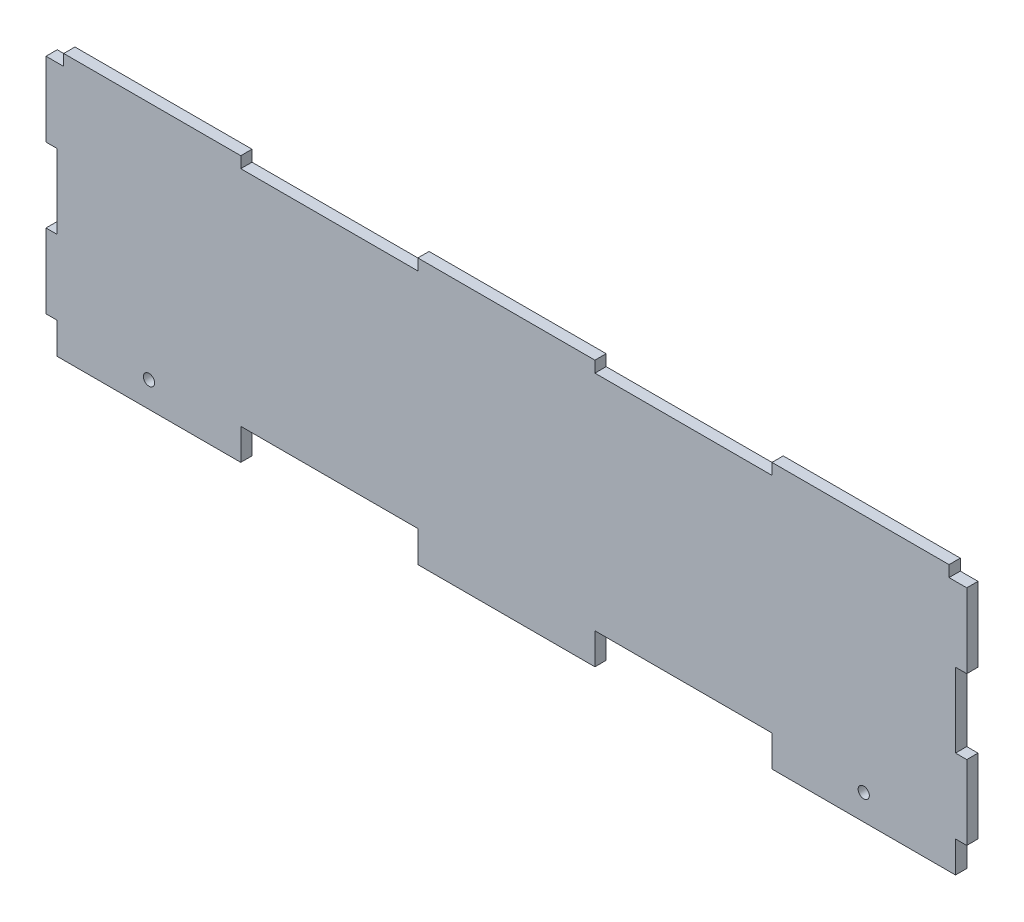
SolidWorks part; units mm, degrees
ref_plane "Front Plane" through (0, 0, 0) normal (0, 0, 1) x (1, 0, 0)
ref_plane "Top Plane" through (0, 0, 0) normal (0, 1, 0) x (1, 0, 0)
ref_plane "Right Plane" through (0, 0, 0) normal (1, 0, 0) x (0, 0, -1)
sketch "Sketch1" plane through (0, 0, 0) normal (0, 0, 1) x (1, 0, 0)
  line L0 (5, 71.825) -> (55, 71.825) construction
  line L1 (0, 75) -> (260, 75)
  line L2 (0, 75) -> (0, 0)
  line L3 (0, 0) -> (260, 0)
  line L4 (260, 75) -> (260, 0)
  line L5 (5, 75) -> (5, 71.825)
  line L6 (255, 75) -> (255, 71.825)
  line L7 (55, 71.825) -> (55, 75)
  line L8 (105, 75) -> (105, 71.825)
  line L9 (105, 71.825) -> (155, 71.825) construction
  line L10 (155, 71.825) -> (155, 75)
  line L11 (205, 71.825) -> (255, 71.825) construction
  line L12 (5, 71.825) -> (0, 71.825)
  line L13 (255, 71.825) -> (260, 71.825)
  line L14 (205, 71.825) -> (205, 75)
  line L15 (256.825, 75) -> (256.825, 0) construction
  line L16 (55, 71.825) -> (105, 71.825)
  line L17 (155, 71.825) -> (205, 71.825)
  line L18 (260, 50.825) -> (256.825, 50.825)
  line L19 (256.825, 50.825) -> (256.825, 29.825)
  line L20 (256.825, 29.825) -> (260, 29.825)
  line L21 (3.175, 75) -> (3.175, 0) construction
  line L22 (3.175, 50.825) -> (0, 50.825)
  line L23 (3.175, 50.825) -> (3.175, 29.825)
  line L24 (3.175, 29.825) -> (0, 29.825)
  line L25 (0, 8.825) -> (260, 8.825) construction
  line L26 (3.175, 0) -> (3.175, 8.825)
  line L27 (256.825, 0) -> (256.825, 8.825)
  line L28 (55, 8.825) -> (55, 0)
  line L29 (105, 8.825) -> (105, 0)
  line L30 (3.175, 8.825) -> (0, 8.825)
  line L31 (155, 8.825) -> (155, 0)
  line L32 (205, 8.825) -> (205, 0)
  line L33 (256.825, 8.825) -> (260, 8.825)
  line L34 (3.175, 7.2375) -> (55, 7.2375) construction
  line L35 (55, 8.825) -> (105, 8.825)
  line L36 (155, 8.825) -> (205, 8.825)
  line L37 (256.825, 7.2375) -> (205, 7.2375) construction
  line L38 (230.9125, 8.825) -> (230.9125, 5.65) construction
  line L39 (29.0875, 8.825) -> (29.0875, 5.65) construction
  line L40 (3.175, 5.65) -> (55, 5.65) construction
  line L41 (205, 5.65) -> (256.825, 5.65) construction
  circle A0 centre (29.0875, 7.2375) radius 1.575
  circle A1 centre (230.9125, 7.2375) radius 1.575
  circle A2 centre (230.9125, 7.2375) radius 3 construction
  circle A3 centre (29.0875, 7.2375) radius 3 construction
  point P14 (230.9125, -17.0449)
  point P55 (230.9125, 25.3199)
  point P58 (230.9125, 5.65)
  point P63 (29.0875, 7.2375)
  point P74 (230.9125, 7.2375)
  dimension "D17" = 3.15
  dimension "D18" = 6
  dimension "D19" = 3.15
  dimension "D20" = 6
  dimension "D10" = 21
  dimension "D1" = 75
  dimension "D2" = 5
  dimension "D3" = 5
  dimension "D4" = 260
  dimension "D5" = 50
  dimension "D6" = 50
  dimension "D7" = 3.175
  dimension "D8" = 3.175
  dimension "D9" = 63
  dimension "D11" = 21
  dimension "D12" = 3.175
  dimension "D13" = 21
  dimension "D14" = 3.175
  dimension "D16" = 8.825
  dimension "D21" = 50
  dimension "D22" = 50
  dimension "D23" = 50
extrude "Boss-Extrude1" add sketch "Sketch1" along normal blind 3.175
